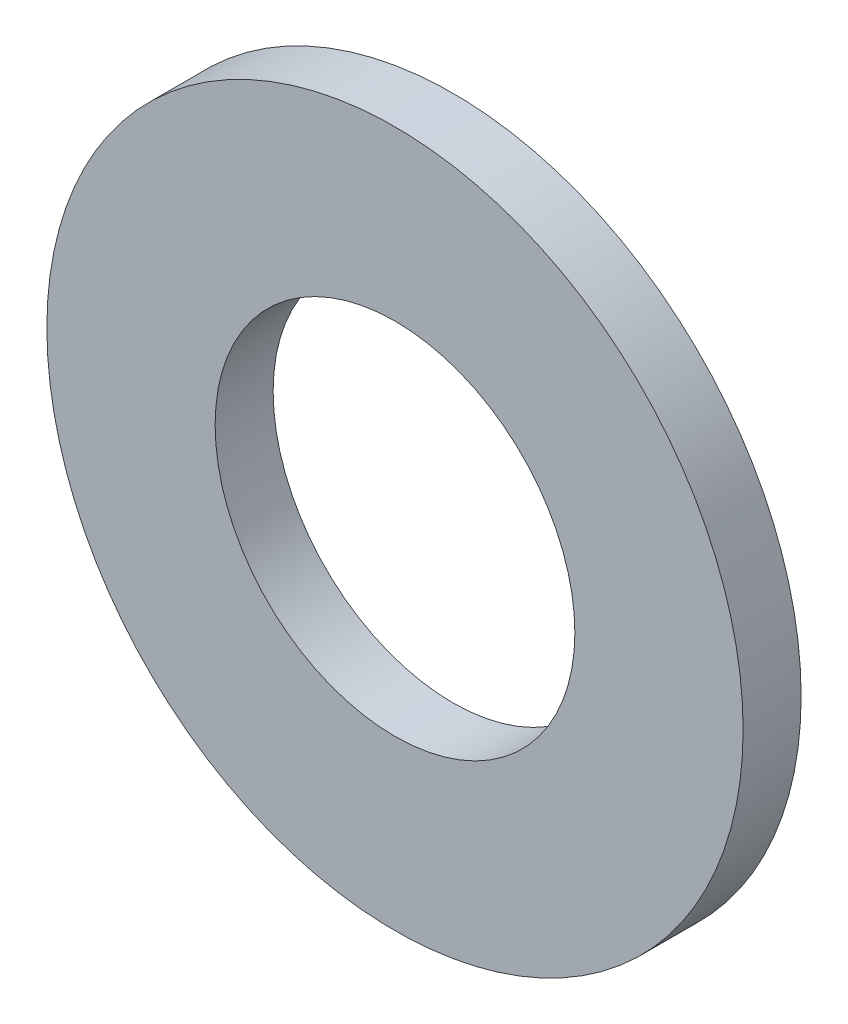
SolidWorks part; units mm, degrees
ref_plane "Front" through (0, 0, 0) normal (0, 0, 1) x (1, 0, 0)
ref_plane "Top" through (0, 0, 0) normal (0, 1, 0) x (1, 0, 0)
ref_plane "Right" through (0, 0, 0) normal (1, 0, 0) x (0, 0, -1)
sketch "Sketch1" plane through (0, 0, 0) normal (0, 0, 1) x (1, 0, 0)
  circle A0 centre (0, 0) radius 4.9213
  circle A1 centre (0, 0) radius 9.525
  dimension "D1" = 9.8425
  dimension "D2" = 19.05
extrude "Extrude1" add sketch "Sketch1" along normal blind 1.5875
